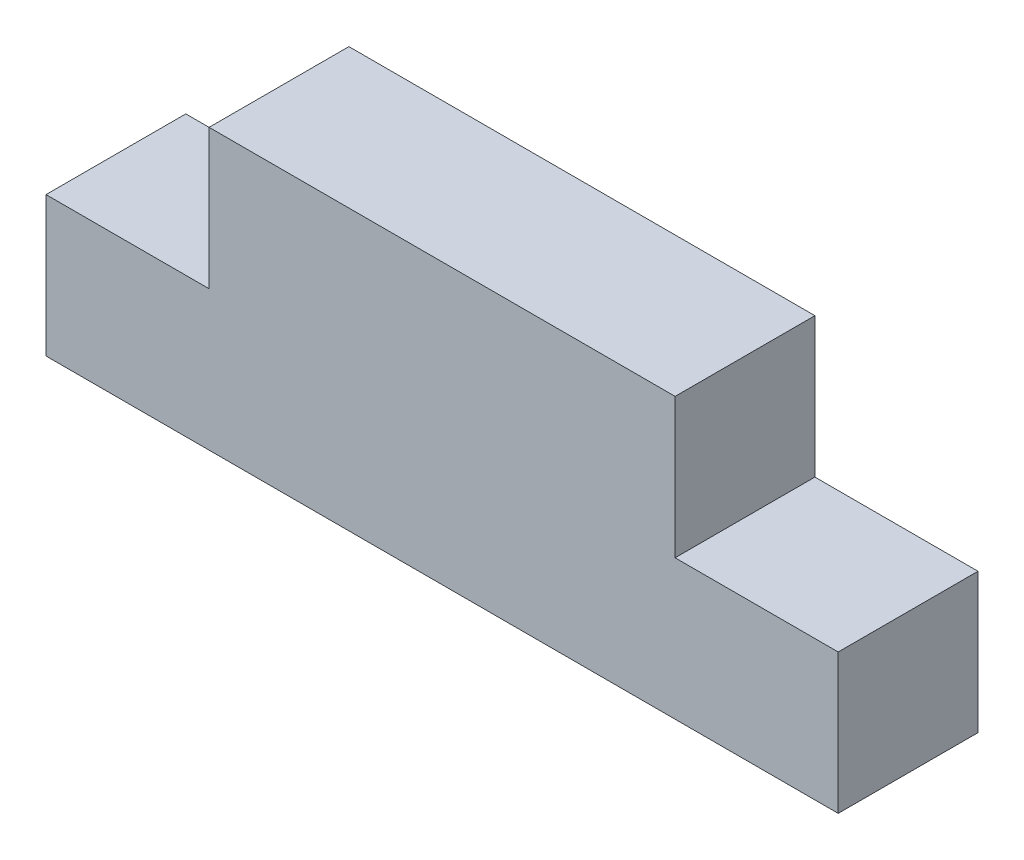
SolidWorks part; units mm, degrees
ref_plane "Plano frontal" through (0, 0, 0) normal (0, 0, 1) x (1, 0, 0)
ref_plane "Plano superior" through (0, 0, 0) normal (0, 1, 0) x (1, 0, 0)
ref_plane "Plano direito" through (0, 0, 0) normal (1, 0, 0) x (0, 0, -1)
sketch "Esboço1" plane through (0, 0, 0) normal (0, 0, 1) x (1, 0, 0)
  line L0 (7, 6) -> (7, 12)
  line L1 (0, 0) -> (34, 0)
  line L2 (0, 0) -> (0, 12)
  line L3 (0, 12) -> (34, 12)
  line L4 (34, 0) -> (34, 12)
  line L5 (0, 12) -> (6, 12)
  line L6 (0, 12) -> (0, 6)
  line L7 (0, 6) -> (7, 6)
  line L9 (34, 12) -> (28, 12)
  line L10 (34, 12) -> (34, 6)
  line L11 (34, 6) -> (27, 6)
  line L13 (27, 6) -> (27, 12)
  point P13 (0, 0)
  dimension "D1" = 12
  dimension "D2" = 20
  dimension "D3" = 6
  dimension "D4" = 7
  dimension "D5" = 7
extrude "Ressalto-extrusão1" add sketch "Esboço1" along normal blind 6
